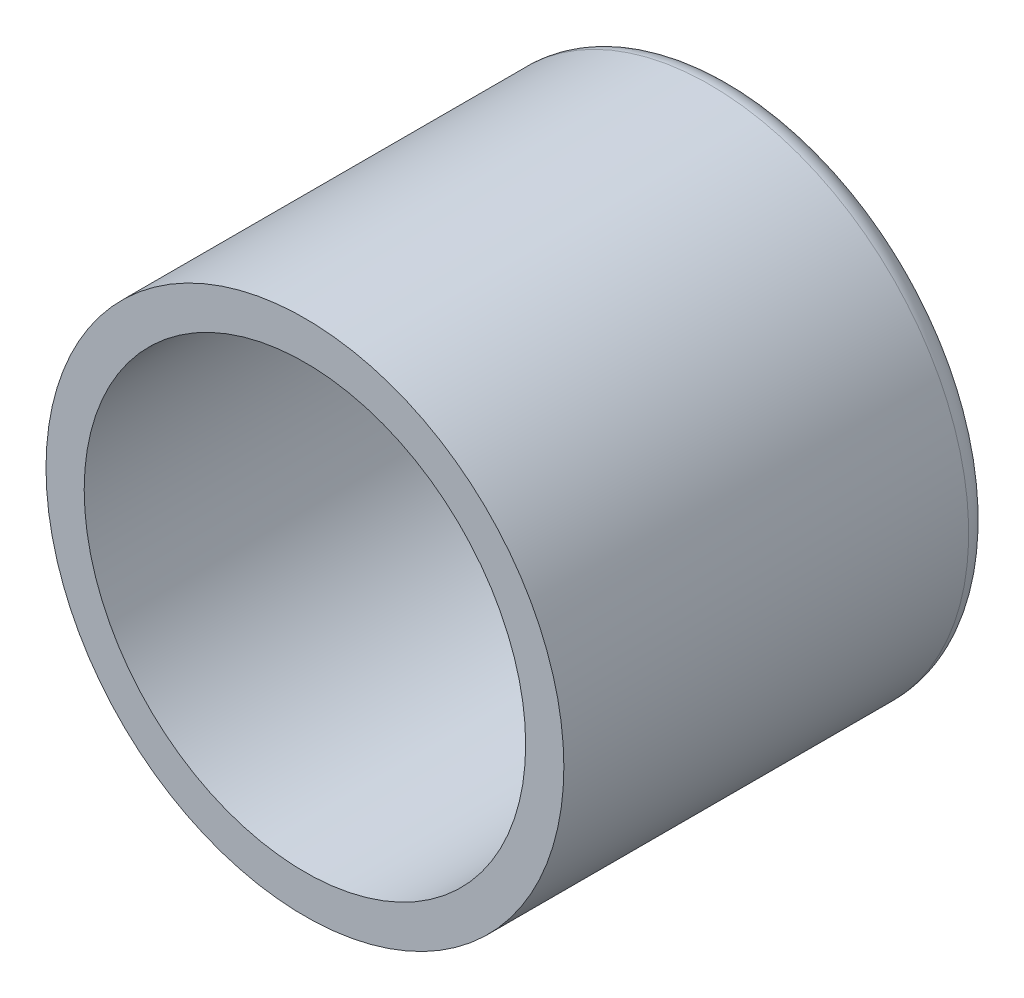
SolidWorks part; units mm, degrees
material "AISI 4130 Steel, annealed at 865C"
ref_plane "Front Plane" through (0, 0, 0) normal (0, 0, 1) x (1, 0, 0)
ref_plane "Top Plane" through (0, 0, 0) normal (0, 1, 0) x (1, 0, 0)
ref_plane "Right Plane" through (0, 0, 0) normal (1, 0, 0) x (0, 0, -1)
sketch "Sketch1" plane through (0, 0, 0) normal (0, 0, 1) x (1, 0, 0)
  circle A0 centre (0, 0) radius 16.95
  circle A1 centre (0, 0) radius 14.45
  dimension "D1" = 33.9
  dimension "D2" = 28.9
extrude "Boss-Extrude1" add sketch "Sketch1" along normal blind 25
sketch "Sketch2" plane through (0, 0, 0) normal (0, 0, -1) x (-1, 0, 0)
  circle A0 centre (0, 0) radius 16.95
extrude "Boss-Extrude2" add sketch "Sketch2" along normal blind 3
fillet "Fillet1" radius 1.5 1 edges at (-16.95, 0, -3)
